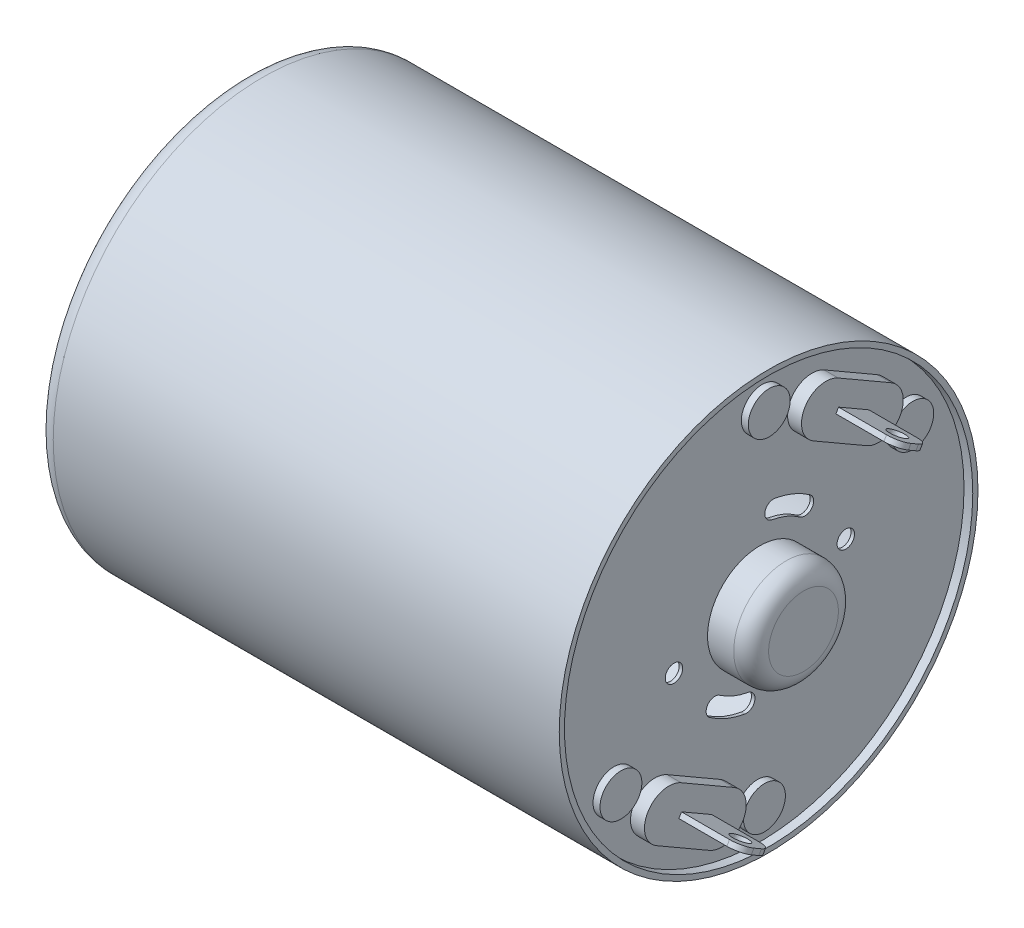
SolidWorks part; units mm, degrees
ref_plane "Front Plane" through (0, 0, 0) normal (0, 0, 1) x (1, 0, 0)
ref_plane "Top Plane" through (0, 0, 0) normal (0, 1, 0) x (1, 0, 0)
ref_plane "Right Plane" through (0, 0, 0) normal (1, 0, 0) x (0, 0, -1)
sketch "Sketch1" plane through (0, 0, 0) normal (1, 0, 0) x (0, 0, -1)
  circle A0 centre (0, 0) radius 12
  circle A1 centre (0, 0) radius 11.7
  dimension "D1" = 0.3
  dimension "D2" = 24
extrude "Boss-Extrude1" add sketch "Sketch1" against normal blind 30
ref_plane "Plane1" through (-0.5, 0, 0) normal (1, 0, 0) x (0, 0, -1)
sketch "Sketch2" plane through (-0.5, 0, 0) normal (1, 0, 0) x (0, 0, -1)
  circle A0 centre (0, 0) radius 11.7
  circle A1 centre (0, 0) radius 11.7 construction
extrude "Boss-Extrude2" add sketch "Sketch2" against normal blind 0.2
sketch "Sketch3" plane through (-0.5, 0, 0) normal (1, 0, 0) x (0, 0, -1)
  circle A0 centre (0, 0) radius 3
  dimension "D1" = 6
extrude "Boss-Extrude3" add sketch "Sketch3" along normal blind 2.5
fillet "Fillet1" radius 1 1 edges at (2, 0, -3)
sketch "Sketch4" plane through (-0.5, 0, 0) normal (1, 0, 0) x (0, 0, -1)
  line L0 (0, 0) -> (0.7814, 4.4316) construction
  line L1 (0, 0) -> (2.5811, 3.6862) construction
  line L2 (0, 0) -> (0, 12) construction
  arc A0 (2.5811, 3.6862) -> (0.7814, 4.4316) centre (0, 0) ccw construction
  arc A1 (2.8679, 4.0958) -> (0.8682, 4.924) centre (0, 0) ccw
  arc A2 (2.2943, 3.2766) -> (0.6946, 3.9392) centre (0, 0) ccw
  arc A3 (2.2943, 3.2766) -> (2.8679, 4.0958) centre (2.5811, 3.6862) ccw
  arc A4 (0.8682, 4.924) -> (0.6946, 3.9392) centre (0.7814, 4.4316) ccw
  circle A5 centre (0, 0) radius 12 construction
  point P4 (1.7221, 4.1575)
  dimension "D1" = 4.5
  dimension "D4" = 0.5
  dimension "D2" = 10
  dimension "D3" = 25
extrude "Cut-Extrude1" cut sketch "Sketch4" against normal through all
pattern_circular "CirPattern1" count 2 over 360 about axis through (0, 0, 0) along (1, 0, 0) of "Cut-Extrude1"
sketch "Sketch5" plane through (-0.5, 0, 0) normal (1, 0, 0) x (0, 0, -1)
  line L0 (0, 0) -> (11.7, 0) construction
  line L1 (0, 0) -> (4.924, 0.8682) construction
  circle A0 centre (4.924, 0.8682) radius 0.5
  circle A1 centre (0, 0) radius 11.7 construction
  dimension "D1" = 1
  dimension "D2" = 10
  dimension "D3" = 5
extrude "Cut-Extrude2" cut sketch "Sketch5" against normal through all
pattern_circular "CirPattern2" count 2 over 360 about axis through (0, 0, 0) along (1, 0, 0) of "Cut-Extrude2"
sketch "Sketch7" plane through (-30, 0, 0) normal (-1, 0, 0) x (0, 0, 1)
  circle A0 centre (0, 0) radius 11.7
  circle A1 centre (0, 0) radius 11.7 construction
extrude "Boss-Extrude4" add sketch "Sketch7" against normal blind 0.3
sketch "Sketch9" plane through (-30, 0, 0) normal (-1, 0, 0) x (0, 0, 1)
  circle A0 centre (0, 0) radius 3
  dimension "D1" = 6
extrude "Cut-Extrude3" cut sketch "Sketch9" against normal up to next
sketch "Sketch6" plane through (-0.5, 0, 0) normal (1, 0, 0) x (0, 0, -1)
  line L0 (2.9845, 8.6692) -> (6.0155, 6.9192) construction
  line L1 (3.6845, 9.8817) -> (6.7155, 8.1317)
  line L2 (2.2845, 7.4568) -> (5.3155, 5.7068)
  line L3 (0, 0) -> (4.5, 7.7942) construction
  line L4 (0, 0) -> (12, 0) construction
  arc A0 (3.6845, 9.8817) -> (2.2845, 7.4568) centre (2.9845, 8.6692) ccw
  arc A1 (5.3155, 5.7068) -> (6.7155, 8.1317) centre (6.0155, 6.9192) ccw
  circle A2 centre (0, 0) radius 12 construction
  point P2 (4.5, 7.7942)
  dimension "D1" = 1.4
  dimension "D2" = 3.5
  dimension "D3" = 60
  dimension "D4" = 9
extrude "Boss-Extrude5" add sketch "Sketch6" along normal blind 0.8
sketch "Sketch10" plane through (-0.5, 0, 0) normal (1, 0, 0) x (0, 0, -1)
  line L0 (0.1364, 9.7362) -> (8.3636, 4.9862) construction
  line L1 (2.2845, 7.4568) -> (5.3155, 5.7068) construction
  line L2 (5.2, 9.0067) -> (4.25, 7.3612) construction
  line L3 (6.7155, 8.1317) -> (3.6845, 9.8817) construction
  circle A0 centre (0.1364, 9.7362) radius 1.2
  circle A1 centre (8.3636, 4.9862) radius 1.2
  arc A2 (3.6845, 9.8817) -> (2.2845, 7.4568) centre (2.9845, 8.6692) ccw construction
  point P6 (1.772, 9.3692)
  dimension "D3" = 2.4
  dimension "D1" = 0.5
  dimension "D2" = 9.5
extrude "Boss-Extrude6" add sketch "Sketch10" along normal blind 0.4
sketch "Sketch11" plane through (0.3, 0, 0) normal (1, 0, 0) x (0, 0, -1)
  line L0 (3.8, 6.5818) -> (5.2, 9.0067) construction
  line L1 (3.709, 8.4241) -> (5.441, 7.4241)
  line L2 (3.709, 8.4241) -> (3.559, 8.1643)
  line L3 (3.559, 8.1643) -> (5.291, 7.1643)
  line L4 (5.441, 7.4241) -> (5.291, 7.1643)
  line L6 (3.709, 8.4241) -> (5.291, 7.1643) construction
  line L7 (3.559, 8.1643) -> (5.441, 7.4241) construction
  line L8 (2.2845, 7.4568) -> (5.3155, 5.7068) construction
  line L9 (6.7155, 8.1317) -> (3.6845, 9.8817) construction
  point P0 (4.5, 7.7942)
  dimension "D1" = 0.3
  dimension "D2" = 2
extrude "Boss-Extrude7" add sketch "Sketch11" along normal blind 3.5
sketch "Sketch12" plane through (0, 7.6643, -4.425) normal (0, -0.866, 0.5) x (-1, 0, 0)
  line L0 (-3.8, 0) -> (-2.8, 0) construction
  line L1 (-3.8, -1) -> (-3.8, 1) construction
  circle A0 centre (-2.8, 0) radius 0.5
  dimension "D2" = 1
  dimension "D1" = 1
extrude "Cut-Extrude4" cut sketch "Sketch12" against normal through all
fillet "Fillet3" radius 0.75 2 edges at (3.8, 8.2942, -3.634) (3.8, 7.2942, -5.366)
pattern_circular "CirPattern3" count 2 over 360 about axis through (0, 0, 0) along (1, 0, 0) of "Boss-Extrude5", "Fillet3", "Boss-Extrude7", "Cut-Extrude4"
sketch "Sketch13" plane through (-30, 0, 0) normal (-1, 0, 0) x (0, 0, 1)
  circle A0 centre (0, 0) radius 3
  circle A1 centre (0, 0) radius 3 construction
extrude "Boss-Extrude8" add sketch "Sketch13" against normal blind 0.3 separate body
sketch "Sketch14" plane through (-30, 0, 0) normal (-1, 0, 0) x (0, 0, 1)
  circle A0 centre (0, 0) radius 1
  dimension "D1" = 2
extrude "Cut-Extrude5" cut sketch "Sketch14" against normal up to next (0.3 mm away)
fillet "Fillet2" radius 1 1 edges at (-30, 0, -12)
pattern_circular "CirPattern4" count 2 over 360 about axis through (0, 0, 0) along (1, 0, 0) of "Boss-Extrude6"
